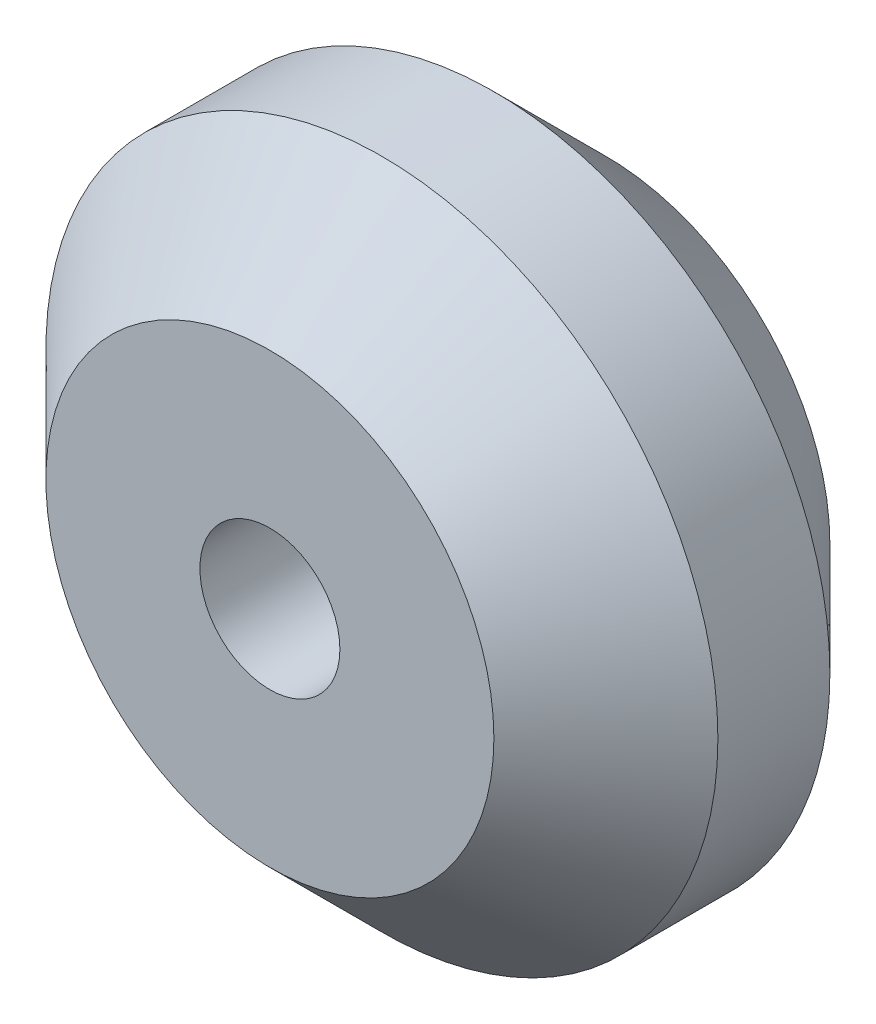
SolidWorks part; units mm, degrees
ref_plane "Front Plane" through (0, 0, 0) normal (0, 0, 1) x (1, 0, 0)
ref_plane "Top Plane" through (0, 0, 0) normal (0, 1, 0) x (1, 0, 0)
ref_plane "Right Plane" through (0, 0, 0) normal (1, 0, 0) x (0, 0, -1)
sketch "Sketch1" plane through (0, 0, 0) normal (0, 0, 1) x (1, 0, 0)
  circle A0 centre (0, 0) radius 2.5
  circle A1 centre (0, 0) radius 12
  dimension "D1" = 24
  dimension "D2" = 5
extrude "Boss-Extrude1" add sketch "Sketch1" along normal blind 12
chamfer "Chamfer1" distance 4 angle 45 2 edges at (12, 0, 0) (12, 0, 12)
